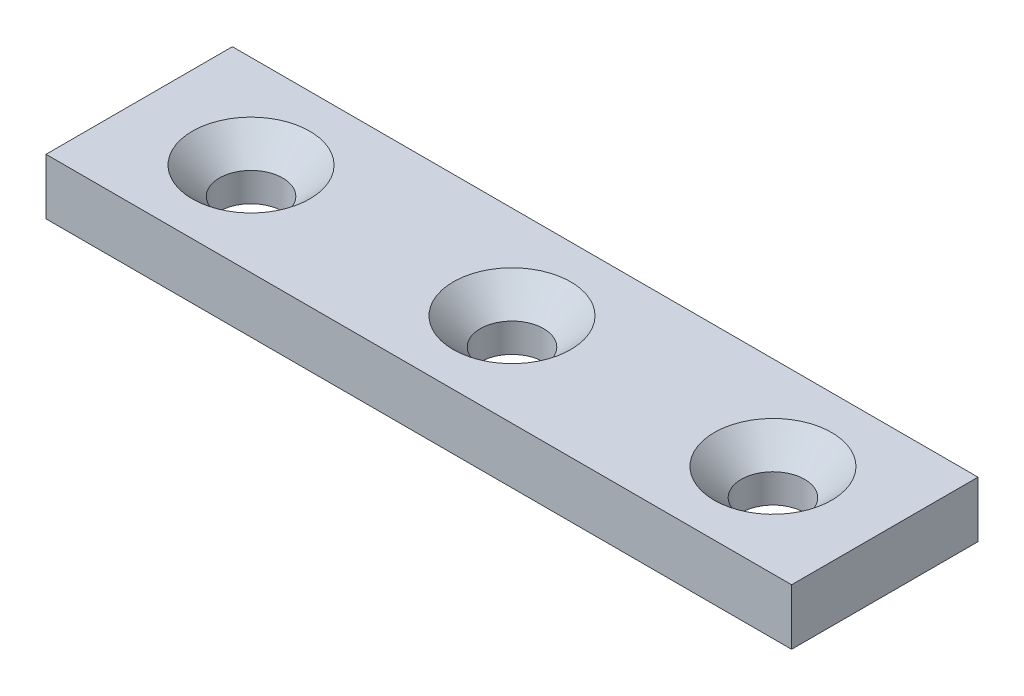
SolidWorks part; units mm, degrees
material "Alloy Steel"
ref_plane "Front Plane" through (0, 0, 0) normal (0, 0, 1) x (1, 0, 0)
ref_plane "Top Plane" through (0, 0, 0) normal (0, 1, 0) x (1, 0, 0)
ref_plane "Right Plane" through (0, 0, 0) normal (1, 0, 0) x (0, 0, -1)
sketch "Sketch1" plane through (0, 0, 0) normal (0, 1, 0) x (1, 0, 0)
  line L1 (-20, -5) -> (20, -5)
  line L2 (-20, -5) -> (-20, 5)
  line L3 (-20, 5) -> (20, 5)
  line L4 (20, -5) -> (20, 5)
  line L5 (-20, -5) -> (20, 5) construction
  line L6 (-20, 5) -> (20, -5) construction
  point P0 (0, 0)
  dimension "D1" = 40
  dimension "D2" = 10
extrude "Boss-Extrude1" add sketch "Sketch1" along normal blind 3
sketch "Sketch2" plane through (0, 3, 0) normal (0, 1, 0) x (1, 0, 0)
  line L0 (-14, 0) -> (14, 0) construction
  point P4 (0, 0)
  point P6 (-14, 0)
  point P7 (14, 0)
  dimension "D1" = 28
hole_wizard "CSK for M3 Countersunk Flat Head Screw1" positions "3DSketch1" profile "Sketch3" countersink size "M3" standard "DIN" end condition through all
sketch3d "3DSketch1"
  point P0 (-14, 3, 0)
  point P3 (14, 3, 0)
  point P6 (0, 3, 0)
sketch "Sketch3" plane through (-14, 3, 0) normal (1, 0, 0) x (0, 0, 1)
  line L0 (0, 0) -> (0, 3)
  line L1 (0, 3) -> (1.7, 3)
  line L2 (1.7, 3) -> (1.7, 1.45)
  line L3 (1.7, 1.45) -> (3.15, 0)
  line L5 (3.15, 0) -> (0, 0)
  line L6 (-1.7, 1.45) -> (-3.15, 0) construction
  line L11 (0, -6.35) -> (0, 107.95) construction
  dimension "Thru Hole Dia." = 3.4
  dimension "Thru Hole Depth" = 3
  dimension "Near C'Sink Dia." = 6.3
  dimension "Near C'Sink Angle" = 90
